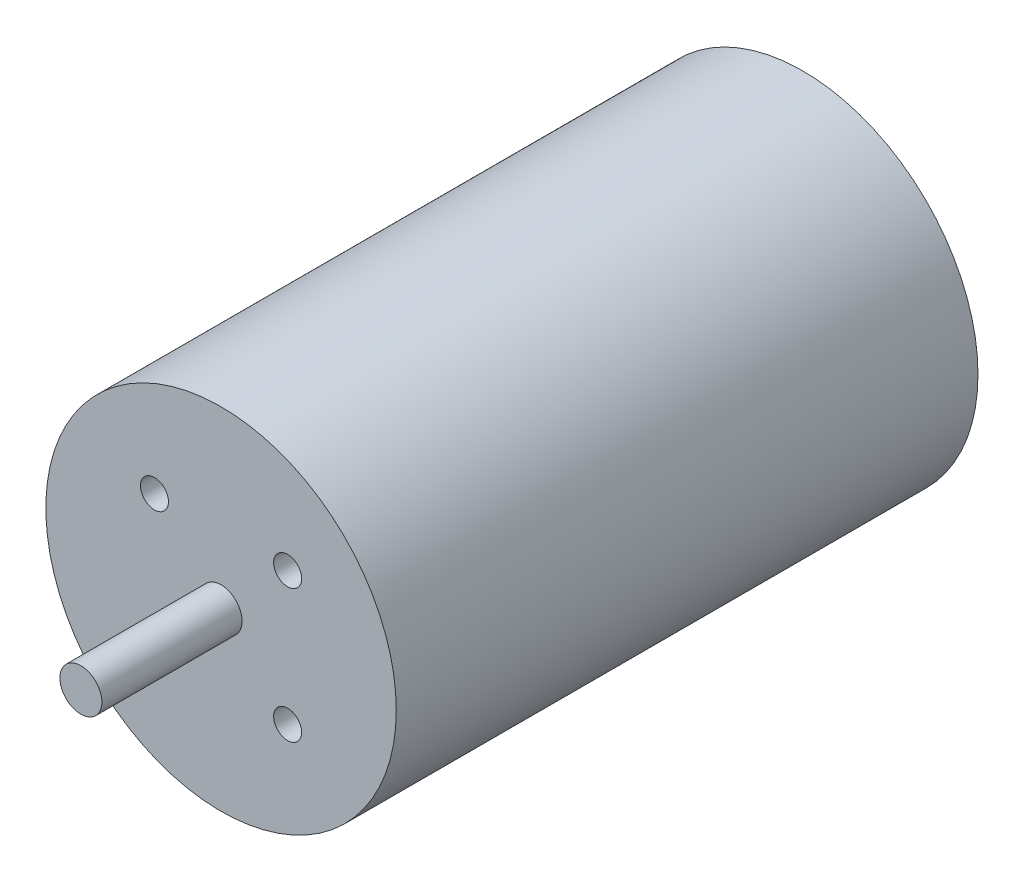
SolidWorks part; units mm, degrees
ref_plane "Front Plane" through (0, 0, 0) normal (0, 0, 1) x (1, 0, 0)
ref_plane "Top Plane" through (0, 0, 0) normal (0, 1, 0) x (1, 0, 0)
ref_plane "Right Plane" through (0, 0, 0) normal (1, 0, 0) x (0, 0, -1)
sketch "Sketch1" plane through (0, 0, 0) normal (0, 0, 1) x (1, 0, 0)
  circle A0 centre (0, 0) radius 25
  dimension "D1" = 50
extrude "Boss-Extrude1" add sketch "Sketch1" along normal blind 83
sketch "Sketch2" plane through (0, 0, 83) normal (0, 0, 1) x (1, 0, 0)
  circle A0 centre (0, 0) radius 3
  dimension "D1" = 6
extrude "Boss-Extrude2" add sketch "Sketch2" along normal blind 20
sketch "Sketch3" plane through (0, 0, 83) normal (0, 0, 1) x (1, 0, 0)
  line L0 (0, 0) -> (-9.5, 0) construction
  line L1 (-9.5, 0) -> (-9.5, 18.0447) construction
  line L2 (0, 0) -> (0, 8.948) construction
  line L3 (9.5, 0) -> (9.5, 18.0447) construction
  line L4 (0, 9.5) -> (-9.5, 9.5) construction
  line L5 (0, -9.5) -> (-9.5, -9.5) construction
  circle A0 centre (-9.5, 9.5) radius 2
  circle A1 centre (-9.5, -9.5) radius 2
  circle A2 centre (9.5, -9.5) radius 2
  circle A3 centre (9.5, 9.5) radius 2
  dimension "D2" = 4
  dimension "D1" = 9.5
extrude "Cut-Extrude1" cut sketch "Sketch3" against normal blind 10
